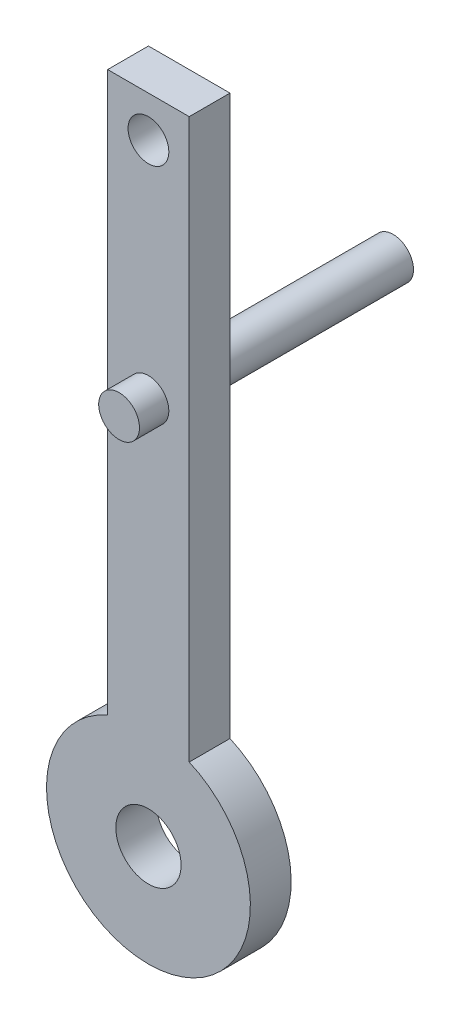
SolidWorks part; units mm, degrees
ref_plane "Front Plane" through (0, 0, 0) normal (0, 0, 1) x (1, 0, 0)
ref_plane "Top Plane" through (0, 0, 0) normal (0, 1, 0) x (1, 0, 0)
ref_plane "Right Plane" through (0, 0, 0) normal (1, 0, 0) x (0, 0, -1)
sketch "Sketch1" plane through (0, 0, 0) normal (0, 0, 1) x (1, 0, 0)
  line L2 (0, 0) -> (0, 68.5436)
  line L3 (0, 68.5436) -> (10, 68.5436)
  line L4 (10, 0) -> (10, 68.5436)
  arc A0 (0, 0) -> (10, 0) centre (5, -11.4564) ccw
  circle A1 centre (5, -11.4564) radius 4
  dimension "D3" = 25
  dimension "D5" = 8
  dimension "D1" = 10
  dimension "D2" = 5
  dimension "D4" = 80
extrude "Boss-Extrude1" add sketch "Sketch1" along normal blind 5
sketch "Sketch2" plane through (0, 0, 5) normal (0, 0, 1) x (1, 0, 0)
  line L1 (10, 68.5436) -> (0, 68.5436) construction
  circle A1 centre (5, 63.5436) radius 2.5
  point P7 (5, 68.5436)
  dimension "D1" = 5
  dimension "D3" = 5
extrude "Cut-Extrude1" cut sketch "Sketch2" against normal through all
sketch "Sketch3" plane through (0, 0, 5) normal (0, 0, 1) x (1, 0, 0)
  line L0 (10, 68.5436) -> (0, 68.5436) construction
  line L1 (0, 68.5436) -> (0, 0) construction
  circle A0 centre (5, 36.0436) radius 2.5
  dimension "D2" = 5
  dimension "D3" = 5
  dimension "D1" = 32.5
extrude "Boss-Extrude2" add sketch "Sketch3" along normal blind 3.6
sketch "Sketch4" plane through (0, 0, 0) normal (0, 0, -1) x (-1, 0, 0)
  line L0 (0, 68.5436) -> (0, 0) construction
  line L1 (-10, 68.5436) -> (0, 68.5436) construction
  circle A0 centre (-5, 36.0436) radius 2.5
  dimension "D2" = 5
  dimension "D1" = 5
  dimension "D3" = 32.5
extrude "Boss-Extrude3" add sketch "Sketch4" along normal blind 25
